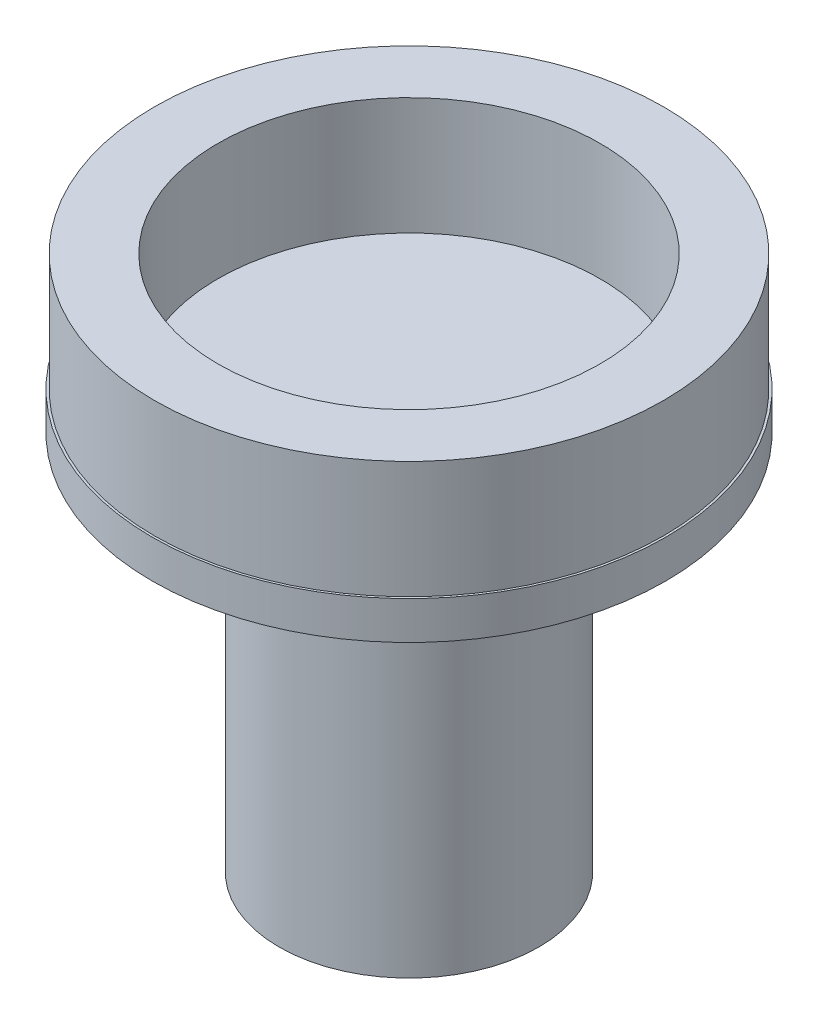
SolidWorks part; units mm, degrees
ref_plane "Front Plane" through (0, 0, 0) normal (0, 0, 1) x (1, 0, 0)
ref_plane "Top Plane" through (0, 0, 0) normal (0, 1, 0) x (1, 0, 0)
ref_plane "Right Plane" through (0, 0, 0) normal (1, 0, 0) x (0, 0, -1)
sketch "Sketch1" plane through (0, 0, 0) normal (0, 1, 0) x (1, 0, 0)
  circle A0 centre (0, 0) radius 3.015
  circle A1 centre (0, 0) radius 4.015
  dimension "D1" = 6.03
  dimension "D2" = 1
extrude "Boss-Extrude1" add sketch "Sketch1" along normal blind 1.85
sketch "Sketch2" plane through (0, 0, 0) normal (0, 1, 0) x (1, 0, 0)
  circle A0 centre (0, 0) radius 4.05
extrude "Boss-Extrude2" add sketch "Sketch2" against normal blind 0.6
sketch "Sketch3" plane through (0, -0.6, 0) normal (0, -1, 0) x (1, 0, 0)
  circle A0 centre (0, 0) radius 1.05
  circle A1 centre (0, 0) radius 2.05
  dimension "D1" = 2.1
  dimension "D2" = 1
extrude "Boss-Extrude3" add sketch "Sketch3" along normal blind 6
